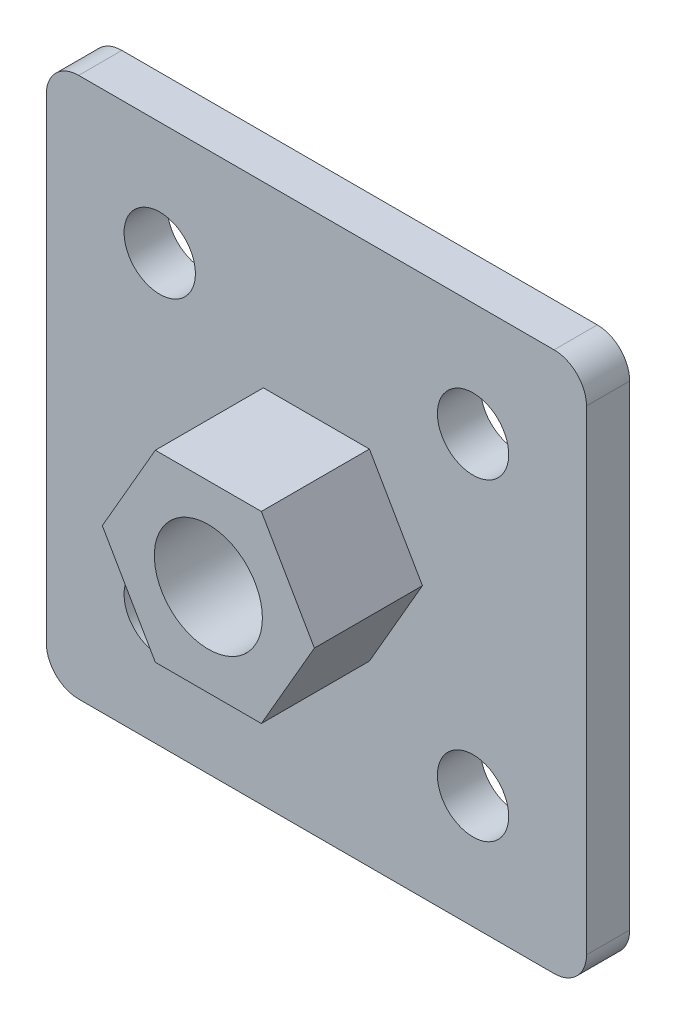
SolidWorks part; units mm, degrees
ref_plane "Спереди" through (0, 0, 0) normal (0, 0, 1) x (1, 0, 0)
ref_plane "Сверху" through (0, 0, 0) normal (0, 1, 0) x (1, 0, 0)
ref_plane "Справа" through (0, 0, 0) normal (1, 0, 0) x (0, 0, -1)
sketch "Эскиз1" plane through (0, 0, 0) normal (0, 0, 1) x (1, 0, 0)
  line L1 (-25, -25) -> (25, -25)
  line L2 (-25, -25) -> (-25, 25)
  line L3 (-25, 25) -> (25, 25)
  line L4 (25, -25) -> (25, 25)
  line L5 (-25, -25) -> (25, 25) construction
  line L6 (-25, 25) -> (25, -25) construction
  point P0 (0, 0)
  dimension "D1" = 50
  dimension "D2" = 50
extrude "Бобышка-Вытянуть1" add sketch "Эскиз1" along normal blind 4
hole_wizard "Отверстие с зазором M101" positions "Эскиз2" profile "Эскиз3" hole size "M10" standard "DIN" end condition through all
sketch "Эскиз2" plane through (0, 0, 4) normal (0, 0, 1) x (1, 0, 0)
  point P0 (0, 0)
sketch "Эскиз3" plane through (0, 0, 4) normal (1, 0, 0) x (0, -1, 0)
  line L0 (0, 0) -> (0, 4)
  line L1 (0, 4) -> (5.5, 4)
  line L2 (5.5, 4) -> (5.5, 0)
  line L5 (5.5, 0) -> (0, 0)
  line L11 (0, -6.35) -> (0, 107.95) construction
  dimension "Диаметр сквозного отверстия" = 11
  dimension "Глубина сквозного отверстия" = 4
fillet "Скругление1" radius 3 4 edges at (-25, 25, 2) (25, 25, 2) (-25, -25, 2) (25, -25, 2)
hole_wizard "Отверстие с зазором M61" positions "Эскиз4" profile "Эскиз5" hole size "M6" standard "DIN" end condition through all
sketch "Эскиз4" plane through (0, 0, 0) normal (0, 0, -1) x (-1, 0, 0)
  line L8 (-14.5, -14.5) -> (14.5, -14.5) construction
  line L9 (-14.5, -14.5) -> (-14.5, 14.5) construction
  line L10 (-14.5, 14.5) -> (14.5, 14.5) construction
  line L11 (14.5, -14.5) -> (14.5, 14.5) construction
  line L12 (-14.5, -14.5) -> (14.5, 14.5) construction
  line L13 (-14.5, 14.5) -> (14.5, -14.5) construction
  point P0 (-14.5, 14.5)
  point P19 (0, 0)
  point P20 (14.5, 14.5)
  point P93 (-14.5, -14.5)
  point P95 (14.5, -14.5)
  dimension "D1" = 29
sketch "Эскиз5" plane through (14.5, 14.5, 0) normal (1, 0, 0) x (0, 1, 0)
  line L0 (0, 0) -> (0, 4)
  line L1 (0, 4) -> (3.3, 4)
  line L2 (3.3, 4) -> (3.3, 0)
  line L5 (3.3, 0) -> (0, 0)
  line L11 (0, -6.35) -> (0, 107.95) construction
  dimension "Диаметр сквозного отверстия" = 6.6
  dimension "Глубина сквозного отверстия" = 4
sketch "Эскиз6" plane through (0, 0, 4) normal (0, 0, 1) x (1, 0, 0)
  line L0 (-22, -25) -> (22, -25) construction
  line L1 (4.9075, -8.5) -> (9.815, 0)
  line L2 (9.815, 0) -> (4.9075, 8.5)
  line L3 (4.9075, 8.5) -> (-4.9075, 8.5)
  line L4 (-4.9075, 8.5) -> (-9.815, 0)
  line L5 (-9.815, 0) -> (-4.9075, -8.5)
  line L6 (-4.9075, -8.5) -> (4.9075, -8.5)
  circle A0 centre (0, 0) radius 8.5 construction
  circle A1 centre (0, 0) radius 5
  dimension "D1" = 10
  dimension "D2" = 17
extrude "Бобышка-Вытянуть2" add sketch "Эскиз6" along normal blind 10
